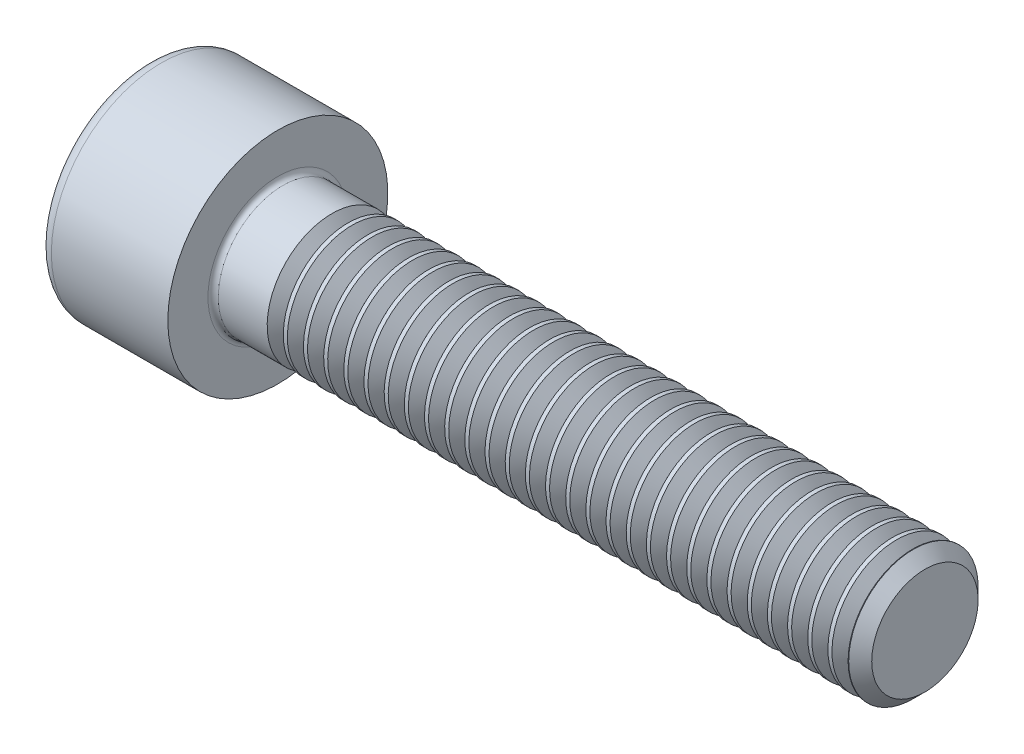
SolidWorks part; units mm, degrees
revolve "Base-Revolve" add sketch "BodySke"
sketch "BodySke" plane through (0, 0, 0) normal (0, 0, 1) x (1, 0, 0)
  line L0 (0, 0) -> (0, 4.25)
  line L1 (0, 4.25) -> (5, 4.25)
  line L2 (5, 4.25) -> (5, 2.5)
  line L3 (5, 2.5) -> (29.555, 2.5)
  line L4 (30, 2.055) -> (30, 0)
  line L5 (30, 0) -> (0, 0)
  line L6 (-31.75, 0) -> (127, 0) construction
  line L8 (30, 2.055) -> (29.555, 2.5)
  line L10 (30, -2.055) -> (29.555, -2.5) construction
  line L11 (5.8, 9.525) -> (5.8, 3.175) construction
  line L12 (5, 9.525) -> (5, 3.175) construction
  line L13 (-30, 9.525) -> (-30, 3.175) construction
  dimension "Body_ch_ang" = 45
  dimension "Advance" = 0.8
  dimension "Thread_length" = 60
cosmetic thread "ThreadCosmetic" [suppressed]
fillet "Fillet1" radius 0.2 1 edges at (5, 0, 2.5)
fillet "Fillet2" radius 0.5 1 edges at (0, 0, 4.25)
ref_plane "Plane1" through (0, 0, 0) normal (0, 0, 1) x (1, 0, 0)
ref_plane "Plane2" through (0, 0, 0) normal (0, 1, 0) x (1, 0, 0)
ref_plane "Plane3" through (0, 0, 0) normal (1, 0, 0) x (0, 0, -1)
sketch "Sketch2" plane through (0, 0, 0) normal (0, 0, 1) x (1, 0, 0)
  line L0 (0, 2.01) -> (2.5, 2.01)
  line L1 (2.5, 2.01) -> (3.6605, 0)
  line L2 (-31.75, 0) -> (127, 0) construction
  line L3 (3.6605, 0) -> (0, 0)
  line L4 (0, 0) -> (0, 2.01)
  line L6 (0, 0) -> (47.625, 0) construction
  dimension "D2" = 60
  dimension "Depth" = 2.5
revolve "Hex-PreBroach" cut sketch "Sketch2" angle 360 about L6
sketch "Sketch3" plane through (0, 0, 0) normal (-1, 0, 0) x (0, 0.5, 0.866)
  line L0 (1.1605, 2.01) -> (-1.1605, 2.01)
  line L1 (-1.1605, 2.01) -> (-2.3209, 0)
  line L2 (1.1605, 2.01) -> (2.3209, 0)
  line L3 (1.1605, -2.01) -> (2.3209, 0)
  line L4 (1.1605, -2.01) -> (-1.1605, -2.01)
  line L5 (-1.1605, -2.01) -> (-2.3209, 0)
extrude "Hex" cut sketch "Sketch3" against normal blind 2.5
sketch "ThdSchSke" plane through (0, 0, 0) normal (0, 0, 1) x (1, 0, 0)
  line L0 (7.4, -2.055) -> (7.0884, -2.5)
  line L1 (7.4, -2.055) -> (7.7116, -2.5)
  line L2 (7.7116, -2.5) -> (7.7116, -3.125)
  line L3 (-3.175, 0) -> (5.1513, 0) construction
  line L4 (0, 3.75) -> (0, -3.75) construction
  line L5 (7.7116, -3.125) -> (7.0884, -3.125)
  line L6 (7.0884, -3.125) -> (7.0884, -2.5)
revolve "ThreadSchematic" cut sketch "ThdSchSke" angle 360 about L3
pattern_linear "ThdSchPat" count 29 spacing 0.7793 along (1, 0, 0) of "ThreadSchematic"
equation "\"D2@Sketch3\" = \"Hex_size@Sketch3\" / 2"
equation "\"D1@Sketch3\" = \"Hex_size@Sketch3\" / 2"
equation "\"D1@Sketch2\" = \"Hex_size@Sketch3\" / 2"
equation "\"Thread_minor@ThreadCosmetic\"  =  \"Minor_dia@BodySke\""
equation "\"Depth@Sketch2\" =  \"Key_eng@Hex\""
equation "\"Thread_length@ThreadCosmetic\" = ((sgn( (\"Length@BodySke\" - \"Advance@BodySke\" * 3.0) - \"Thread_nom@BodySke\" )-1)*( (\"Length@BodySke\" - \"Advance@BodySke\" * 3.0) - \"Thread_nom@BodySke\" ))/-2+ \"Thread_nom@BodySke\""
equation "\"Thread_minor@ThdSchSke\" = \"Minor_dia@BodySke\""
equation "\"Diameter@ThdSchSke\" = \"Diameter@BodySke\""
equation "\"Overcut@ThdSchSke\" = \"Diameter@BodySke\" * 1.25"
equation "\"Start@ThdSchSke\" = \"Head_ht@BodySke\" + \"Length@BodySke\" - \"Thread_length@ThreadCosmetic\"  '---Non-countersunk---"
equation "\"Num_threads@ThdSchPat\" = int( \"Thread_length@ThreadCosmetic\" / \"Advance@BodySke\" + 0.999 )  + 1"
equation "\"Advance@ThdSchPat\" = \"Thread_length@ThreadCosmetic\" /  (\"Num_threads@ThdSchPat\" - 1) 'relax it"
equation "\"Num_threads@ThdSchPat\" = \"Num_threads@ThdSchPat\" - sgn( \"Num_threads@ThdSchPat\" - 1) '---chamfered tips only---"
